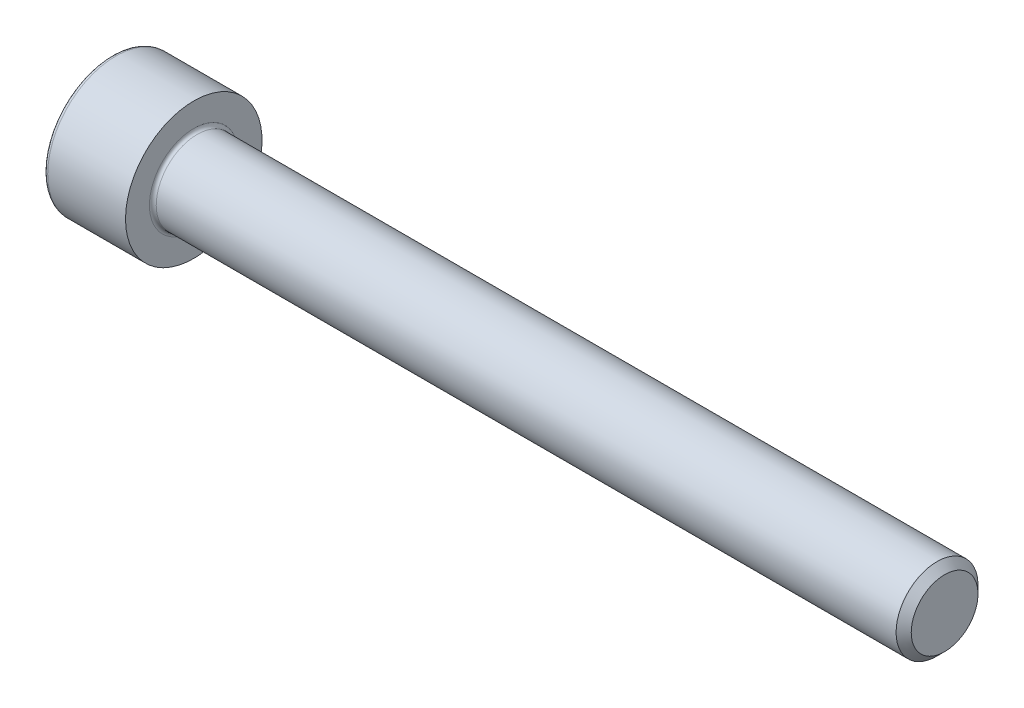
SolidWorks part; units mm, degrees
revolve "Base-Revolve" add sketch "BodySke"
sketch "BodySke" plane through (0, 0, 0) normal (0, 0, 1) x (1, 0, 0)
  line L0 (0, 0) -> (0, 5)
  line L1 (0, 5) -> (6, 5)
  line L2 (6, 5) -> (6, 3)
  line L3 (6, 3) -> (60.4455, 3)
  line L4 (61, 2.4455) -> (61, 0)
  line L5 (61, 0) -> (0, 0)
  line L6 (-31.75, 0) -> (127, 0) construction
  line L8 (61, 2.4455) -> (60.4455, 3)
  line L10 (61, -2.4455) -> (60.4455, -3) construction
  line L11 (7, 9.525) -> (7, 3.175) construction
  line L12 (37, 9.525) -> (37, 3.175) construction
  line L13 (1, 9.525) -> (1, 3.175) construction
  dimension "Body_ch_ang" = 45
  dimension "Thread_length" = 60
cosmetic thread "ThreadCosmetic" [suppressed]
fillet "Fillet1" radius 0.25 1 edges at (6, 0, 3)
fillet "Fillet2" radius 0.3 1 edges at (0, 0, 5)
ref_plane "Plane1" through (0, 0, 0) normal (0, 0, 1) x (1, 0, 0)
ref_plane "Plane2" through (0, 0, 0) normal (0, 1, 0) x (1, 0, 0)
ref_plane "Plane3" through (0, 0, 0) normal (1, 0, 0) x (0, 0, -1)
sketch "Sketch2" plane through (0, 0, 0) normal (0, 0, 1) x (1, 0, 0)
  line L0 (0, 2.542) -> (3, 2.542)
  line L1 (3, 2.542) -> (4.4676, 0)
  line L2 (-31.75, 0) -> (127, 0) construction
  line L3 (4.4676, 0) -> (0, 0)
  line L4 (0, 0) -> (0, 2.542)
  line L6 (0, 0) -> (47.625, 0) construction
  dimension "D2" = 60
revolve "Hex-PreBroach" cut sketch "Sketch2" angle 360 about L6
sketch "Sketch3" plane through (0, 0, 0) normal (-1, 0, 0) x (0, 0.5, 0.866)
  line L0 (1.4676, 2.542) -> (-1.4676, 2.542)
  line L1 (-1.4676, 2.542) -> (-2.9352, 0)
  line L2 (1.4676, 2.542) -> (2.9352, 0)
  line L3 (1.4676, -2.542) -> (2.9352, 0)
  line L4 (1.4676, -2.542) -> (-1.4676, -2.542)
  line L5 (-1.4676, -2.542) -> (-2.9352, 0)
extrude "Hex" cut sketch "Sketch3" against normal blind 3
sketch "ThdSchSke" plane through (0, 0, 0) normal (0, 0, 1) x (1, 0, 0)
  line L0 (37, -2.4455) -> (36.6117, -3)
  line L1 (37, -2.4455) -> (37.3883, -3)
  line L2 (37.3883, -3) -> (37.3883, -3.75)
  line L3 (-3.175, 0) -> (5.1513, 0) construction
  line L4 (0, 4.7) -> (0, -4.7) construction
  line L5 (37.3883, -3.75) -> (36.6117, -3.75)
  line L6 (36.6117, -3.75) -> (36.6117, -3)
revolve "ThreadSchematic" [suppressed] cut sketch "ThdSchSke" angle 360 about L3
pattern_linear "ThdSchPat" [suppressed]
equation "\"D2@Sketch3\" = \"Hex_size@Sketch3\" / 2"
equation "\"D1@Sketch3\" = \"Hex_size@Sketch3\" / 2"
equation "\"D1@Sketch2\" = \"Hex_size@Sketch3\" / 2"
equation "\"Thread_minor@ThreadCosmetic\"  =  \"Minor_dia@BodySke\""
equation "\"Depth@Sketch2\" =  \"Key_eng@Hex\""
equation "\"Thread_length@ThreadCosmetic\" = ((sgn( (\"Length@BodySke\" - \"Advance@BodySke\" * 3.0) - \"Thread_nom@BodySke\" )-1)*( (\"Length@BodySke\" - \"Advance@BodySke\" * 3.0) - \"Thread_nom@BodySke\" ))/-2+ \"Thread_nom@BodySke\""
equation "\"Thread_minor@ThdSchSke\" = \"Minor_dia@BodySke\""
equation "\"Diameter@ThdSchSke\" = \"Diameter@BodySke\""
equation "\"Overcut@ThdSchSke\" = \"Diameter@BodySke\" * 1.25"
equation "\"Start@ThdSchSke\" = \"Head_ht@BodySke\" + \"Length@BodySke\" - \"Thread_length@ThreadCosmetic\"  '---Non-countersunk---"
equation "\"Num_threads@ThdSchPat\" = int( \"Thread_length@ThreadCosmetic\" / \"Advance@BodySke\" + 0.999 )  + 1"
equation "\"Advance@ThdSchPat\" = \"Thread_length@ThreadCosmetic\" /  (\"Num_threads@ThdSchPat\" - 1) 'relax it"
equation "\"Num_threads@ThdSchPat\" = \"Num_threads@ThdSchPat\" - sgn( \"Num_threads@ThdSchPat\" - 1) '---chamfered tips only---"
